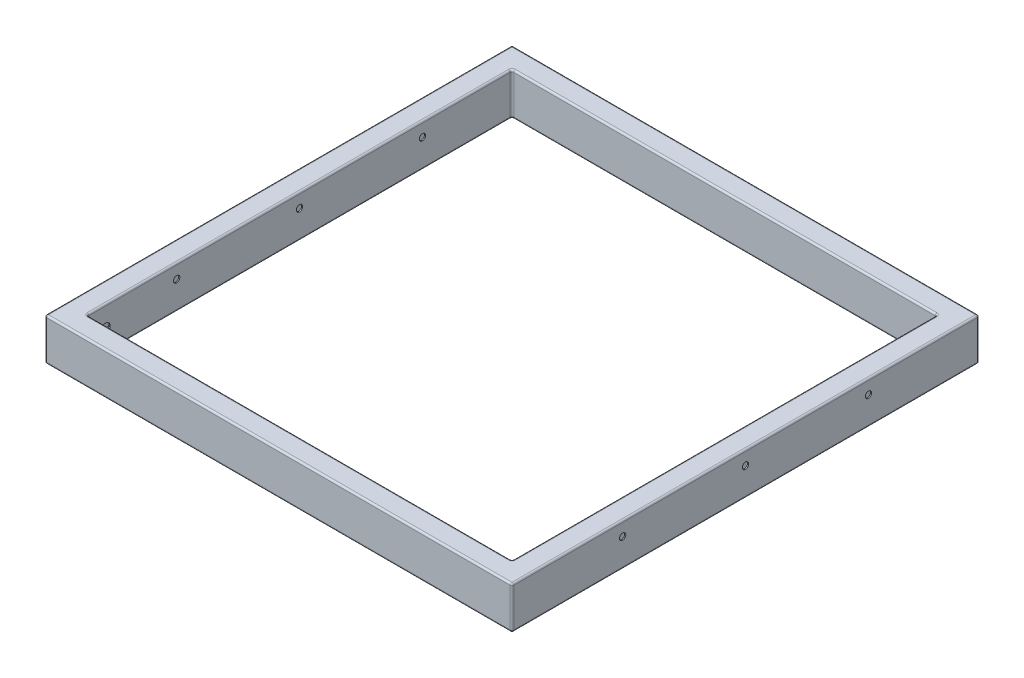
SolidWorks part; units mm, degrees
material "Plain Carbon Steel"
ref_plane "Front" through (0, 0, 0) normal (0, 0, 1) x (1, 0, 0)
ref_plane "Top" through (0, 0, 0) normal (0, 1, 0) x (1, 0, 0)
ref_plane "Right" through (0, 0, 0) normal (1, 0, 0) x (0, 0, -1)
sketch "Sketch1" plane through (0, 0, 0) normal (0, 1, 0) x (1, 0, 0)
  line L1 (-665, 665) -> (665, 665)
  line L2 (-665, 665) -> (-665, -665)
  line L3 (-665, -665) -> (665, -665)
  line L4 (665, 665) -> (665, -665)
  line L5 (-665, 665) -> (665, -665) construction
  line L6 (-665, -665) -> (665, 665) construction
  line L7 (-605, 605) -> (605, 605)
  line L8 (-605, 605) -> (-605, -605)
  line L9 (-605, -605) -> (605, -605)
  line L10 (605, 605) -> (605, -605)
  line L11 (-605, 605) -> (605, -605) construction
  line L12 (-605, -605) -> (605, 605) construction
  point P0 (0, 0)
  point P6 (0, 0)
  dimension "D1" = 1330
  dimension "D2" = 60
extrude "Boss-Extrude1" add sketch "Sketch1" along normal blind 120
fillet "Fillet1" radius 5 24 edges at (-665, 60, 665) (665, 60, 665) (0, 0, 665) (0, 120, 665) (-665, 120, 0) (0, 120, -665) (665, 120, 0) (-605, 120, 0) (0, 120, 605) (605, 120, 0) (0, 120, -605) (665, 60, -665) (-665, 60, -665) (-665, 0, 0) (0, 0, -665) (665, 0, 0) (605, 60, -605) (-605, 60, -605) (-605, 60, 605) (605, 60, 605) (0, 0, 605) (-605, 0, 0) (0, 0, -605) (605, 0, 0)
shell "Shell1" thickness 3
sketch "Sketch3" plane through (665, 0, 0) normal (1, 0, 0) x (0, 0, -1)
  circle A0 centre (350, 80) radius 9
  circle A1 centre (0, 80) radius 9
  circle A2 centre (-350, 80) radius 9
  dimension "D1" = 18
extrude "Cut-Extrude1" cut sketch "Sketch3" against normal through all
sketch "Sketch4" plane through (-665, 0, 0) normal (-1, 0, 0) x (0, 0, 1)
  line L0 (500, 60) -> (605, 60) construction
  line L1 (500, 120) -> (500, -1514) construction
  line L2 (605, 60.5) -> (605, -60.5) construction
  line L3 (660, 0) -> (-660, 0) construction
  circle A0 centre (552.5, 60) radius 13
  dimension "D2" = 26
  dimension "D1" = 60
extrude "Cut-Extrude2" cut sketch "Sketch4" against normal up to surface (60 mm away) up to face at (-605, 80, -359)
